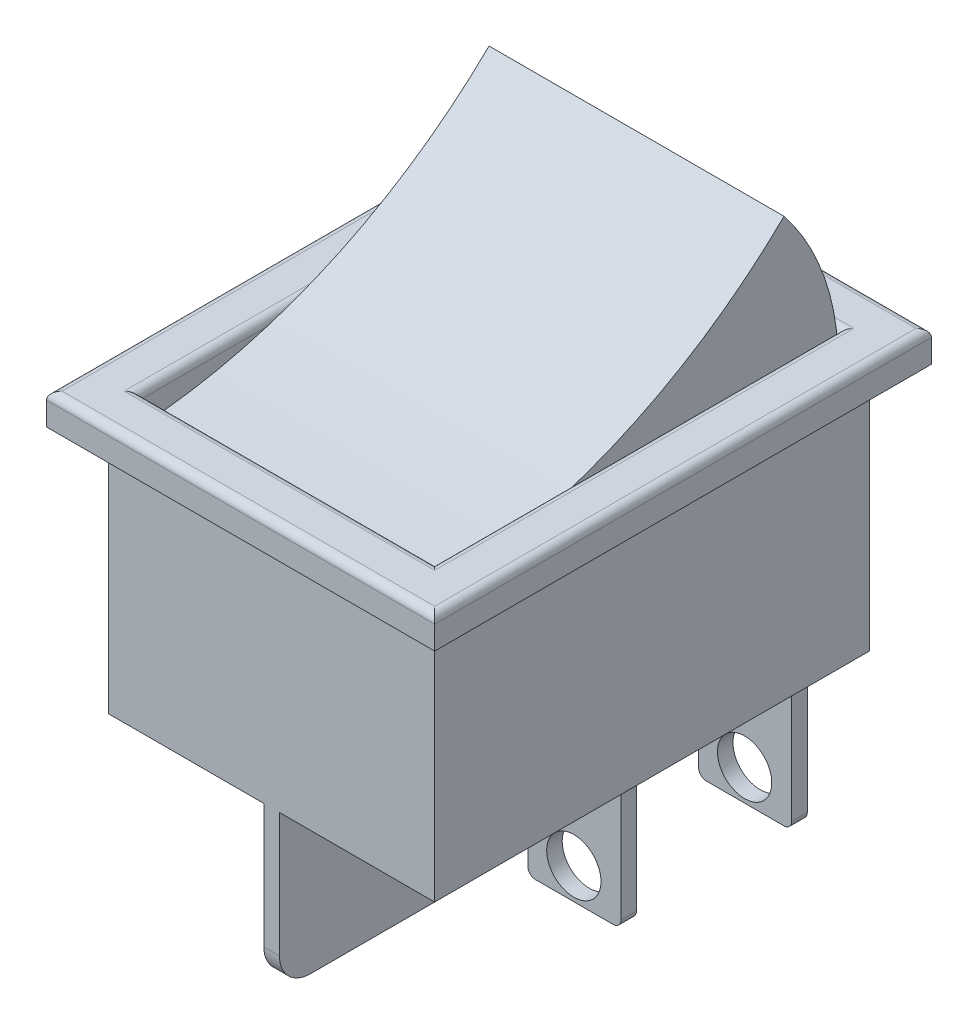
SolidWorks part; units mm, degrees
ref_plane "Front Plane" through (0, 0, 0) normal (0, 0, 1) x (1, 0, 0)
ref_plane "Top Plane" through (0, 0, 0) normal (0, 1, 0) x (1, 0, 0)
ref_plane "Right Plane" through (0, 0, 0) normal (1, 0, 0) x (0, 0, -1)
sketch "Sketch1" plane through (0, 0, 0) normal (0, 1, 0) x (1, 0, 0)
  line L1 (-10.5, -14) -> (10.5, -14)
  line L2 (-10.5, -14) -> (-10.5, 14)
  line L3 (-10.5, 14) -> (10.5, 14)
  line L4 (10.5, -14) -> (10.5, 14)
  line L5 (-10.5, -14) -> (10.5, 14) construction
  line L6 (-10.5, 14) -> (10.5, -14) construction
  point P0 (0, 0)
  dimension "D1" = 28
  dimension "D2" = 21
extrude "Boss-Extrude1" add sketch "Sketch1" along normal blind 16
sketch "Sketch2" plane through (0, 16, 0) normal (0, 1, 0) x (1, 0, 0)
  line L4 (9.5, -13) -> (9.5, 13)
  line L5 (9.5, 13) -> (-9.5, 13)
  line L6 (-9.5, 13) -> (-9.5, -13)
  line L7 (-9.5, -13) -> (9.5, -13)
  line L8 (12.5, -16) -> (12.5, 16)
  line L9 (12.5, 16) -> (-12.5, 16)
  line L10 (-12.5, 16) -> (-12.5, -16)
  line L11 (-12.5, -16) -> (12.5, -16)
  line L12 (12.5, -16) -> (12.5, 16)
  line L13 (12.5, 16) -> (-12.5, 16)
  line L14 (-12.5, 16) -> (-12.5, -16)
  line L15 (-12.5, -16) -> (12.5, -16)
  dimension "D1" = 2
  dimension "D2" = 3
extrude "Boss-Extrude2" add sketch "Sketch2" along normal blind 2
fillet "Fillet1" radius 0.5 8 edges at (0, 18, -13) (-9.5, 18, 0) (0, 18, 13) (9.5, 18, 0) (-12.5, 18, 0) (0, 18, -16) (12.5, 18, 0) (0, 18, 16)
sketch "Sketch3" plane through (0, 0, 0) normal (0, -1, 0) x (1, 0, 0)
  line L0 (-10.5, 14) -> (10.5, 14) construction
  line L1 (-0.5, -14) -> (0.5, -14)
  line L2 (-0.5, -14) -> (-0.5, 14)
  line L3 (-0.5, 14) -> (0.5, 14)
  line L4 (0.5, -14) -> (0.5, 14)
  line L5 (-0.5, -14) -> (0.5, 14) construction
  line L6 (-0.5, 14) -> (0.5, -14) construction
  point P0 (0, 0)
  dimension "D1" = 1
extrude "Boss-Extrude3" add sketch "Sketch3" along normal blind 10
sketch "Sketch4" plane through (0, 0, 0) normal (0, -1, 0) x (1, 0, 0)
  line L0 (-8.5, -12) -> (-8.5, -11)
  line L5 (5.5, 0) -> (5.5, -1) construction
  line L6 (10.5, 14) -> (10.5, -14) construction
  line L11 (0.5, -14) -> (0.5, 14) construction
  line L13 (2.5, -1) -> (8.5, -1)
  line L14 (2.5, -1) -> (2.5, 0)
  line L15 (2.5, 0) -> (8.5, 0)
  line L16 (8.5, -1) -> (8.5, 0)
  line L17 (2.5, -1) -> (8.5, 0) construction
  line L18 (2.5, 0) -> (8.5, -1) construction
  line L23 (-8.5, -1) -> (-8.5, 0)
  line L24 (-8.5, -1) -> (-2.5, -1)
  line L25 (-2.5, -1) -> (-2.5, 0)
  line L26 (-8.5, 0) -> (-2.5, 0)
  line L27 (-5.5, 0) -> (-5.5, -1) construction
  line L28 (-0.5, 14) -> (-0.5, -14) construction
  line L29 (-10.5, -14) -> (-10.5, 14) construction
  line L30 (-8.5, -11) -> (-2.5, -11)
  line L31 (-2.5, -12) -> (-2.5, -11)
  line L32 (-8.5, -12) -> (-2.5, -12)
  line L33 (2.5, -12) -> (2.5, -11)
  line L34 (2.5, -12) -> (8.5, -12)
  line L35 (8.5, -12) -> (8.5, -11)
  line L36 (2.5, -11) -> (8.5, -11)
  line L37 (-0.5, -14) -> (-10.5, -14) construction
  line L39 (10.5, -14) -> (0.5, -14) construction
  point P10 (5.5, -0.5)
  dimension "D1" = 1
  dimension "D2" = 6
  dimension "D3" = 14
  dimension "D6" = 2
  dimension "D4" = 2
  dimension "D5" = 2
extrude "Boss-Extrude4" add sketch "Sketch4" along normal blind 9.5 separate body
sketch "Sketch5" plane through (0, 0, -12) normal (0, 0, -1) x (-1, 0, 0)
  line L1 (-2.5, -9.5) -> (-8.5, -9.5) construction
  line L3 (8.5, -9.5) -> (2.5, -9.5) construction
  line L4 (-5.4638, -0.7215) -> (-5.4638, -2.7215) construction
  line L5 (5.4605, -0.5) -> (5.3326, -2.3854) construction
  circle A0 centre (5.4605, -1.5) radius 1
  circle A1 centre (5.4605, -7.5) radius 1.75
  circle A2 centre (-5.4638, -1.7215) radius 1
  circle A3 centre (-5.4638, -7.5) radius 1.75
  dimension "D1" = 3.5
  dimension "D2" = 2
  dimension "D3" = 0.25
  dimension "D4" = 7
  dimension "D5" = 7
extrude "Cut-Extrude1" cut sketch "Sketch5" against normal through all
fillet "Fillet2" radius 2 2 edges at (0, -10, -14) (0, -10, 14)
fillet "Fillet3" radius 0.5 2 edges at (2.5, -9.5, -11.5) (8.5, -9.5, -11.5)
fillet "Fillet4" radius 0.5 2 edges at (-8.5, -9.5, -11.5) (-2.5, -9.5, -11.5)
fillet "Fillet5" radius 0.5 2 edges at (2.5, -9.5, -0.5) (8.5, -9.5, -0.5)
fillet "Fillet6" radius 0.5 2 edges at (-8.5, -9.5, -0.5) (-2.5, -9.5, -0.5)
sketch "Sketch6" plane through (0, 0, 0) normal (1, 0, 0) x (0, 0, -1)
  line L0 (-13, 16) -> (13, 16)
  line L1 (13, 17.5) -> (13, 16) construction
  line L2 (-16, 16) -> (16, 16) construction
  arc A0 (-13, 16) -> (9.5044, 26) centre (-15.2454, 51.3755) ccw
  arc A1 (9.5044, 26) -> (13, 16) centre (-3.0515, 16) cw
  dimension "D1" = 10
extrude "Boss-Extrude5" add sketch "Sketch6" along normal mid plane 19 separate body
